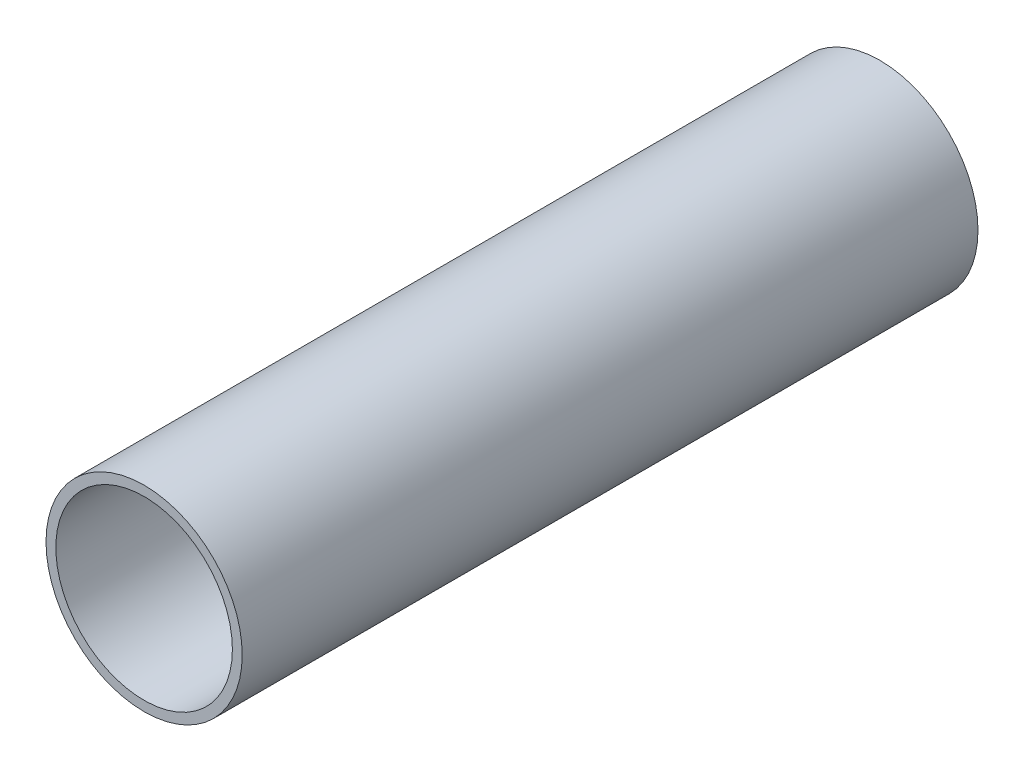
SolidWorks part; units mm, degrees
ref_plane "Front Plane" through (0, 0, 0) normal (0, 0, 1) x (1, 0, 0)
ref_plane "Top Plane" through (0, 0, 0) normal (0, 1, 0) x (1, 0, 0)
ref_plane "Right Plane" through (0, 0, 0) normal (1, 0, 0) x (0, 0, -1)
sketch "Sketch2" plane through (0, 0, 0) normal (0, 0, 1) x (1, 0, 0)
  circle A0 centre (0, 0) radius 20
  circle A1 centre (0, 0) radius 18
  dimension "D1" = 40
  dimension "D2" = 2
extrude "Boss-Extrude1" add sketch "Sketch2" along normal blind 150
